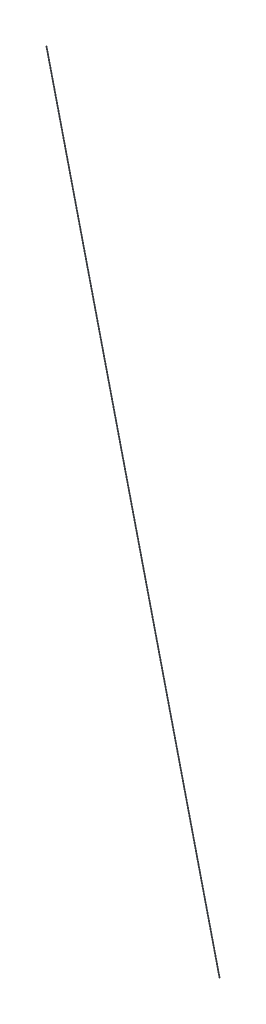
SolidWorks part; units mm, degrees
ref_plane "前视基准面" through (0, 0, 0) normal (0, 0, 1) x (1, 0, 0)
ref_plane "上视基准面" through (0, 0, 0) normal (0, 1, 0) x (1, 0, 0)
ref_plane "右视基准面" through (0, 0, 0) normal (1, 0, 0) x (0, 0, -1)
sketch "草图1" plane through (0, 0, 0) normal (0, 1, 0) x (1, 0, 0)
  line L0 (0, 0) -> (307.5, 0)
sketch "草图2" plane through (0, 0, 0) normal (0, 0, 1) x (1, 0, 0)
  line L0 (0, 0) -> (0, 1279.38)
sketch "草图3" plane through (0, 0, 0) normal (0, 0, 1) x (1, 0, 0)
  line L0 (307.5, 0) -> (0, 1279.38)
  line L1 (0, 0) -> (307.5, 0) construction
sweep "扫描3" add path "草图3" circular profile diameter 1 parameters "D3"=1
